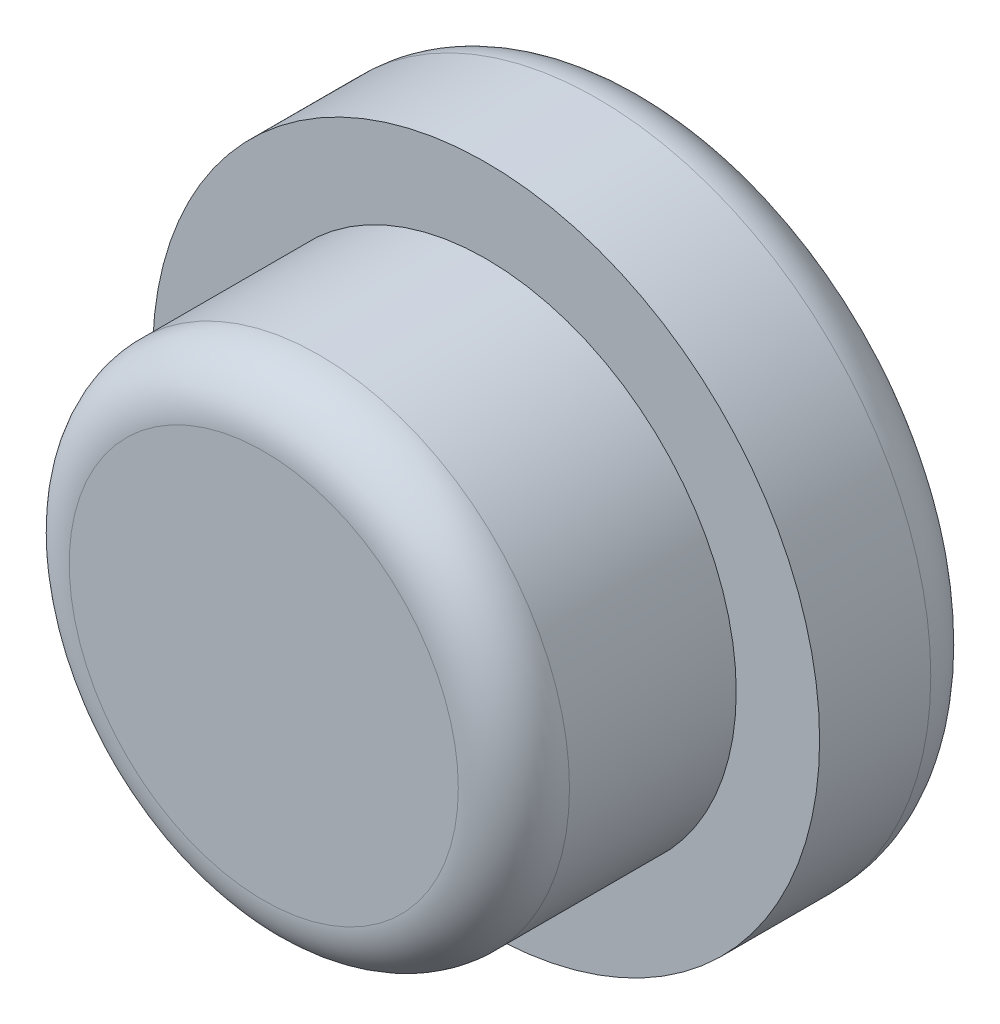
SolidWorks part; units mm, degrees
ref_plane "Спереди" through (0, 0, 0) normal (0, 0, 1) x (1, 0, 0)
ref_plane "Сверху" through (0, 0, 0) normal (0, 1, 0) x (1, 0, 0)
ref_plane "Справа" through (0, 0, 0) normal (1, 0, 0) x (0, 0, -1)
sketch "Эскиз1" plane through (0, 0, 0) normal (0, 0, 1) x (1, 0, 0)
  circle A0 centre (0, 0) radius 3
  dimension "D1" = 6
extrude "Бобышка-Вытянуть1" add sketch "Эскиз1" along normal blind 1.5
sketch "Эскиз2" plane through (0, 0, 1.5) normal (0, 0, 1) x (1, 0, 0)
  circle A0 centre (0, 0) radius 2.25
  dimension "D1" = 4.5
extrude "Бобышка-Вытянуть2" add sketch "Эскиз2" along normal blind 2
sketch "Эскиз3" plane through (0, 0, 0) normal (0, 0, -1) x (-1, 0, 0)
  circle A0 centre (0, 0) radius 1.5
  dimension "D1" = 3
extrude "Вырез-Вытянуть1" cut sketch "Эскиз3" against normal blind 0.5
fillet "Скругление1" radius 0.25 1 edges at (-1.5, 0, 0.5)
fillet "Скругление2" radius 0.5 1 edges at (2.25, 0, 3.5)
fillet "Скругление3" radius 0.5 1 edges at (3, 0, 0)
